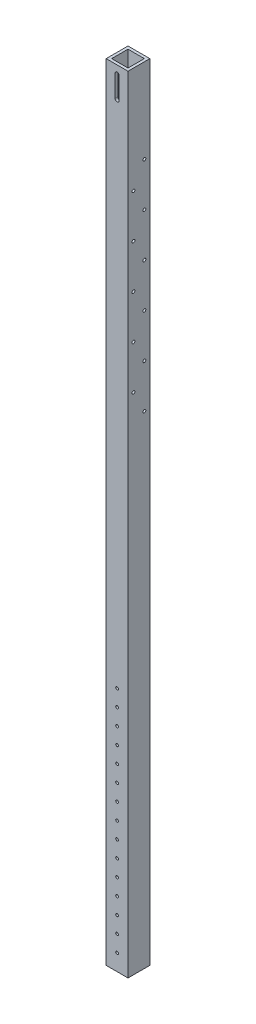
SolidWorks part; units mm, degrees
material "6061-T6 (SS)"
ref_plane "Front Plane" through (0, 0, 0) normal (0, 0, 1) x (1, 0, 0)
ref_plane "Top Plane" through (0, 0, 0) normal (0, 1, 0) x (1, 0, 0)
ref_plane "Right Plane" through (0, 0, 0) normal (1, 0, 0) x (0, 0, -1)
sketch "Sketch1" plane through (0, 0, 0) normal (0, 1, 0) x (1, 0, 0)
  line L0 (9.525, 9.525) -> (-9.525, 9.525)
  line L1 (12.7, -12.7) -> (-12.7, -12.7)
  line L2 (12.7, -12.7) -> (12.7, 12.7)
  line L3 (12.7, 12.7) -> (-12.7, 12.7)
  line L4 (-12.7, -12.7) -> (-12.7, 12.7)
  line L5 (12.7, -12.7) -> (-12.7, 12.7) construction
  line L6 (12.7, 12.7) -> (-12.7, -12.7) construction
  line L7 (-9.525, -9.525) -> (-9.525, 9.525)
  line L8 (9.525, -9.525) -> (-9.525, -9.525)
  line L9 (9.525, -9.525) -> (9.525, 9.525)
  point P0 (0, 0)
  dimension "D1" = 25.4
  dimension "D2" = 3.175
extrude "Boss-Extrude1" add sketch "Sketch1" along normal blind 914.4
sketch "Sketch2" plane through (0, 0, 12.7) normal (0, 0, -1) x (-1, 0, 0)
  line L0 (0, 879.475) -> (0, 904.875) construction
  line L1 (-2.3812, 879.475) -> (-2.3812, 904.875)
  line L2 (2.3812, 879.475) -> (2.3812, 904.875)
  line L3 (-12.7, 914.4) -> (12.7, 914.4) construction
  arc A0 (-2.3812, 879.475) -> (2.3812, 879.475) centre (0, 879.475) ccw
  arc A1 (2.3812, 904.875) -> (-2.3812, 904.875) centre (0, 904.875) ccw
  point P3 (0, 892.175)
  dimension "D2" = 9.525
  dimension "D1" = 4.7625
  dimension "D3" = 25.4
extrude "Cut-Extrude1" cut sketch "Sketch2" along normal up to next
sketch "Sketch3" plane through (0, 0, 12.7) normal (0, 0, 1) x (1, 0, 0)
  line L0 (0, 895.35) -> (0, 825.5) construction
  line L1 (3.175, 895.35) -> (3.175, 825.5)
  line L2 (-3.175, 895.35) -> (-3.175, 825.5)
  line L3 (-12.7, 914.4) -> (12.7, 914.4) construction
  arc A0 (3.175, 895.35) -> (-3.175, 895.35) centre (0, 895.35) ccw
  arc A1 (-3.175, 825.5) -> (3.175, 825.5) centre (0, 825.5) ccw
  point P3 (0, 860.425)
  dimension "D2" = 19.05
  dimension "D1" = 6.35
  dimension "D3" = 69.85
extrude "Cut-Extrude2" [suppressed] cut sketch "Sketch3" against normal up to next
sketch "Sketch4" plane through (-12.7, 0, 0) normal (-1, 0, 0) x (0, 0, 1)
  circle A1 centre (-6.35, 561.975) radius 1.7145 construction
  circle A2 centre (6.35, 587.375) radius 1.7145 construction
  circle A3 centre (-6.35, 612.775) radius 1.7145 construction
  circle A4 centre (6.35, 638.175) radius 1.7145 construction
  circle A5 centre (-6.35, 663.575) radius 1.7145 construction
  circle A6 centre (6.35, 688.975) radius 1.7145 construction
  circle A7 centre (-6.35, 714.375) radius 1.7145 construction
  circle A8 centre (6.35, 739.775) radius 1.7145 construction
  circle A9 centre (-6.35, 765.175) radius 1.7145 construction
  circle A10 centre (6.35, 790.575) radius 1.7145 construction
  circle A11 centre (-6.35, 815.975) radius 1.7145 construction
  circle A12 centre (-6.35, 561.975) radius 1.7145
  circle A13 centre (6.35, 587.375) radius 1.7145
  circle A14 centre (-6.35, 612.775) radius 1.7145
  circle A15 centre (6.35, 638.175) radius 1.7145
  circle A16 centre (-6.35, 663.575) radius 1.7145
  circle A17 centre (6.35, 688.975) radius 1.7145
  circle A18 centre (-6.35, 714.375) radius 1.7145
  circle A19 centre (6.35, 739.775) radius 1.7145
  circle A20 centre (-6.35, 765.175) radius 1.7145
  circle A21 centre (6.35, 790.575) radius 1.7145
  circle A22 centre (-6.35, 815.975) radius 1.7145
extrude "Cut-Extrude3" cut sketch "Sketch4" against normal through all
sketch "Sketch5" plane through (-12.7, 0, 0) normal (-1, 0, 0) x (0, 0, 1)
  line L0 (-12.7, 914.4) -> (-12.7, 0) construction
  line L1 (-12.7, 914.4) -> (12.7, 914.4) construction
  line L2 (-12.7, 914.4) -> (-12.7, 876.3) construction
  circle A0 centre (0, 904.875) radius 4.7625
  circle A1 centre (0, 885.825) radius 4.7625
  dimension "D1" = 9.525
  dimension "D2" = 12.7
  dimension "D3" = 9.525
  dimension "D4" = 38.1
  dimension "D5" = 9.525
extrude "Cut-Extrude4" [suppressed] cut sketch "Sketch5" against normal up to next
sketch "Sketch6" plane through (0, 0, 12.7) normal (0, 0, 1) x (1, 0, 0)
  line L0 (-12.7, 0) -> (-12.7, 304.8) construction
  line L1 (-12.7, 914.4) -> (-12.7, 0) construction
  line L2 (-12.7, 0) -> (12.7, 0) construction
  line L3 (12.7, 914.4) -> (12.7, 0) construction
  circle A28 centre (0, 19.05) radius 1.5875
  circle A29 centre (0, 38.1) radius 1.5875
  circle A30 centre (0, 57.15) radius 1.5875
  circle A31 centre (0, 76.2) radius 1.5875
  circle A32 centre (0, 95.25) radius 1.5875
  circle A33 centre (0, 114.3) radius 1.5875
  circle A34 centre (0, 133.35) radius 1.5875
  circle A35 centre (0, 152.4) radius 1.5875
  circle A36 centre (0, 171.45) radius 1.5875
  circle A37 centre (0, 190.5) radius 1.5875
  circle A38 centre (0, 209.55) radius 1.5875
  circle A39 centre (0, 228.6) radius 1.5875
  circle A40 centre (0, 247.65) radius 1.5875
  circle A41 centre (0, 266.7) radius 1.5875
  circle A42 centre (0, 285.75) radius 1.5875
  dimension "D3" = 19.05
  dimension "D5" = 15
  dimension "D6" = 19.05
  dimension "D2" = 3.175
  dimension "D4" = 12.7
  dimension "D1" = 304.8
extrude "Cut-Extrude5" cut sketch "Sketch6" against normal through all
